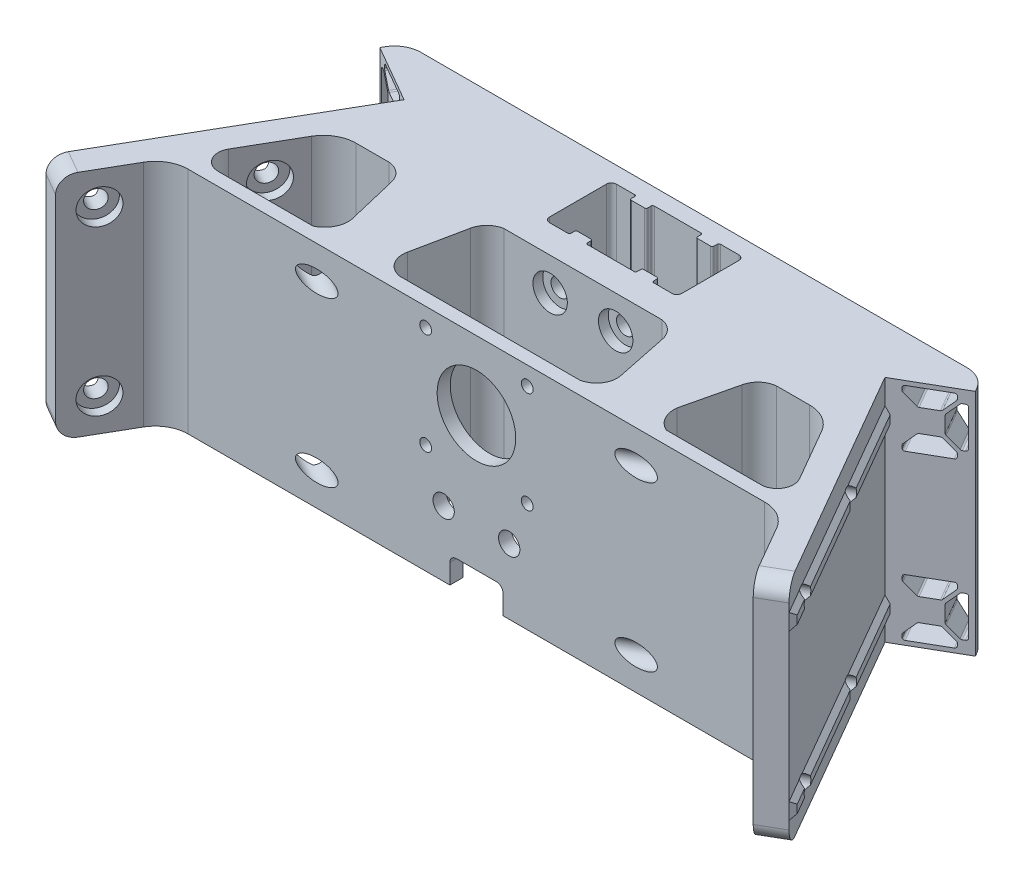
SolidWorks part; units mm, degrees
ref_plane "Front Plane" through (0, 0, 0) normal (0, 0, 1) x (1, 0, 0)
ref_plane "Top Plane" through (0, 0, 0) normal (0, 1, 0) x (1, 0, 0)
ref_plane "Right Plane" through (0, 0, 0) normal (1, 0, 0) x (0, 0, -1)
sketch "Sketch1" plane through (0, 0, 0) normal (0, 1, 0) x (1, 0, 0)
  line L0 (0, -61.4) -> (0, -111.1933) construction
  line L1 (0, 0) -> (-7.6, 0) construction
  line L2 (0, 0) -> (0, -20.4) construction
  line L3 (0, -20.4) -> (-7.1, -20.4) construction
  line L4 (-20.2, 0) -> (-20.2, -20.4) construction
  line L5 (0, 5) -> (-83.3812, 5)
  line L6 (-90.3094, 1) -> (-90.8868, 0)
  line L7 (-90.8868, 0) -> (-73.393, -10.1)
  line L8 (-73.393, -10.1) -> (-113.393, -79.382)
  line L9 (-113.393, -79.382) -> (-106.4648, -83.382)
  line L10 (-106.4648, -83.382) -> (-96.6603, -66.4)
  line L11 (-69.2361, -28.9) -> (0, -28.9)
  line L12 (0, -57.4) -> (0, -61.4)
  line L13 (0, -20.4) -> (-7.1, -20.4)
  line L14 (-20.2, -18.9) -> (-20.2, -1.5)
  line L15 (-18.7, 0) -> (-13.1, 0)
  line L16 (-82.8038, -57.4) -> (0, -57.4)
  line L17 (0, -20.4) -> (0, -28.9)
  line L18 (0, -61.4) -> (-88, -61.4)
  line L19 (-87.134, -49.9) -> (-77.8964, -33.9)
  line L20 (0, 0) -> (0, -20.4) construction
  line L21 (-7.6, -0.5) -> (-7.6, -1.5)
  line L22 (-20.2, -10.2) -> (0, -10.2) construction
  line L23 (-8.1, -2) -> (-12.1, -2)
  line L24 (-12.6, -0.5) -> (-12.6, -1.5)
  line L25 (-12.6, -19.9) -> (-12.6, -18.9)
  line L26 (-8.1, -18.4) -> (-12.1, -18.4)
  line L27 (-12.6, 0) -> (-20.2, 0) construction
  line L28 (-7.1, 0) -> (0, 0)
  line L29 (-7.6, -19.9) -> (-7.6, -18.9)
  line L30 (-13.1, -20.4) -> (-20.2, -20.4) construction
  line L31 (-13.1, -20.4) -> (-18.7, -20.4)
  line L32 (0, -28.9) -> (0, -57.4) construction
  line L33 (0, 5) -> (0, 0)
  arc A0 (-88, -61.4) -> (-96.6603, -66.4) centre (-88, -71.4) ccw
  arc A1 (-77.8964, -33.9) -> (-69.2361, -28.9) centre (-69.2361, -38.9) cw
  arc A2 (-82.8038, -57.4) -> (-87.134, -49.9) centre (-82.8038, -52.4) cw
  arc A3 (-83.3812, 5) -> (-90.3094, 1) centre (-83.3812, -3) ccw
  arc A4 (-7.1, 0) -> (-7.6, -0.5) centre (-7.1, -0.5) ccw
  arc A5 (-12.6, -0.5) -> (-13.1, 0) centre (-13.1, -0.5) ccw
  arc A6 (-7.6, -1.5) -> (-8.1, -2) centre (-8.1, -1.5) cw
  arc A7 (-12.1, -2) -> (-12.6, -1.5) centre (-12.1, -1.5) cw
  arc A8 (-20.2, -1.5) -> (-18.7, 0) centre (-18.7, -1.5) cw
  arc A9 (-18.7, -20.4) -> (-20.2, -18.9) centre (-18.7, -18.9) cw
  arc A10 (-12.1, -18.4) -> (-12.6, -18.9) centre (-12.1, -18.9) ccw
  arc A11 (-7.6, -18.9) -> (-8.1, -18.4) centre (-8.1, -18.9) ccw
  arc A12 (-12.6, -19.9) -> (-13.1, -20.4) centre (-13.1, -19.9) cw
  arc A13 (-7.1, -20.4) -> (-7.6, -19.9) centre (-7.1, -19.9) cw
  point P24 (-91.4641, -57.4)
  point P27 (-88, 5)
  point P30 (-10.1, 0)
  point P63 (-10.1, -20.4)
  dimension "D13" = 10
  dimension "D14" = 5
  dimension "D15" = 8
  dimension "D17" = 0.5
  dimension "D18" = 1.5
  dimension "D1" = 20.2
  dimension "D2" = 20.4
  dimension "D3" = 5
  dimension "D4" = 88
  dimension "D5" = 120
  dimension "D6" = 5
  dimension "D7" = 20.2
  dimension "D8" = 80
  dimension "D9" = 8
  dimension "D10" = 8.5
  dimension "D11" = 4
  dimension "D12" = 37
  dimension "D16" = 5
extrude "Boss-Extrude2" add sketch "Sketch1" along normal blind 70
sketch "Sketch2" plane through (-50.6714, 0, -29.2551) normal (-0.866, 0, -0.5) x (-0.5, 0, 0.866)
  line L0 (45.4434, 70) -> (45.4434, 0) construction
  line L1 (45.4434, 62.5) -> (125.4434, 62.5)
  line L2 (45.4434, 62.5) -> (45.4434, 57.5)
  line L3 (45.4434, 57.5) -> (125.4434, 57.5)
  line L4 (125.4434, 62.5) -> (125.4434, 57.5)
  line L5 (125.4434, 70) -> (125.4434, 0) construction
  line L6 (45.4434, 70) -> (125.4434, 70) construction
  line L7 (45.4434, 35) -> (125.4434, 35) construction
  line L8 (125.4434, 7.5) -> (125.4434, 12.5)
  line L9 (45.4434, 12.5) -> (125.4434, 12.5)
  line L10 (45.4434, 7.5) -> (45.4434, 12.5)
  line L11 (45.4434, 7.5) -> (125.4434, 7.5)
  dimension "D1" = 5
  dimension "D2" = 7.5
extrude "Boss-Extrude3" add sketch "Sketch2" along normal blind 1.5 draft 40
hole_wizard "CBORE for M5 SHCS2" positions "Sketch5" profile "Sketch4" counterbore size "M5" standard "ANSI Metric" end condition up to next
sketch "Sketch5" plane through (-43.7431, 0, -25.2551) normal (0.866, 0, 0.5) x (0.5, 0, -0.866)
  line L0 (-125.4434, 60) -> (-68.3064, 60) construction
  line L1 (-125.4434, 70) -> (-125.4434, 0) construction
  line L2 (-68.3064, 70) -> (-68.3064, 0) construction
  line L4 (-86.7817, 70) -> (-68.3064, 70) construction
  line L5 (-125.4434, 10) -> (-68.3064, 10) construction
  line L7 (-125.4434, 0) -> (-105.8342, 0) construction
  line L10 (-125.4434, 70) -> (-105.8342, 70) construction
  line L11 (-115.6388, 70) -> (-115.6388, 60) construction
  line L13 (-77.5441, 70) -> (-77.5441, 60) construction
  point P0 (-77.5441, 60)
  point P2 (-77.5441, 10)
  point P4 (-115.6388, 60)
  point P6 (-115.6388, 10)
  dimension "D1" = 10
  dimension "D2" = 10
sketch "Sketch4" plane through (-82.5152, 60, 41.9) normal (0, 1, 0) x (0.5, 0, -0.866)
  line L0 (0, 0) -> (0, 9.5)
  line L1 (0, 9.5) -> (2.75, 9.5)
  line L3 (2.75, 9.5) -> (2.75, 3)
  line L4 (2.75, 3) -> (5.25, 3)
  line L5 (5.25, 3) -> (5.25, 0)
  line L7 (5.25, 0) -> (0, 0)
  line L11 (0, -6.35) -> (0, 107.95) construction
  dimension "Thru Hole Dia." = 5.5
  dimension "Thru Hole Depth" = 9.5
  dimension "C'Bore Dia." = 10.5
  dimension "C'Bore Depth" = 3
hole_wizard "CBORE for M5 SHCS3" positions "Sketch7" profile "Sketch6" counterbore size "M5" standard "ANSI Metric" end condition up to next
sketch "Sketch7" plane through (0, 0, 28.9) normal (0, 0, 1) x (1, 0, 0)
  line L0 (0, 60) -> (0, 0) construction
  line L1 (-69.2361, 70) -> (0, 70) construction
  line L2 (-69.2361, 0) -> (0, 0) construction
  line L4 (0, 60) -> (-28.3411, 60)
  line L6 (0, 20) -> (-25.3792, 20) construction
  line L8 (-69.2361, 0) -> (0, 0) construction
  line L10 (0, 70) -> (0, 0) construction
  point P0 (-10, 20)
  point P2 (-10, 60)
  dimension "D1" = 10
  dimension "D2" = 10
  dimension "D3" = 20
sketch "Sketch6" plane through (-10, 20, 28.9) normal (1, 0, 0) x (0, -1, 0)
  line L0 (0, 0) -> (0, 10.5)
  line L1 (0, 10.5) -> (2.75, 10.5)
  line L3 (2.75, 10.5) -> (2.75, 3)
  line L4 (2.75, 3) -> (5.25, 3)
  line L5 (5.25, 3) -> (5.25, 0)
  line L7 (5.25, 0) -> (0, 0)
  line L11 (0, -6.35) -> (0, 107.95) construction
  dimension "Thru Hole Dia." = 5.5
  dimension "Thru Hole Depth" = 10.5
  dimension "C'Bore Dia." = 10.5
  dimension "C'Bore Depth" = 3
chamfer "Chamfer1" [suppressed] distance 5 angle 45
chamfer "Chamfer2" [suppressed] distance 5 angle 45
fillet "Fillet1" radius 5 2 edges at (-109.9289, 0, 81.382) (-109.9289, 70, 81.382)
sketch "Sketch14" plane through (-22.7217, 0, 39.3551) normal (-0.5, 0, 0.866) x (0.866, 0, 0.5)
  line L0 (-73.9972, 68.5) -> (-63.0232, 68.5)
  line L1 (-62.5152, 67.992) -> (-62.5152, 67.2661)
  line L2 (-65.7671, 63.8038) -> (-62.664, 66.9069)
  line L3 (-66.1263, 63.655) -> (-70.8942, 63.655)
  line L12 (-74.5052, 67.992) -> (-74.5052, 67.2661)
  line L13 (-74.3564, 66.9069) -> (-71.2534, 63.8038)
  line L14 (-77.0102, 65.487) -> (-77.0102, 54.513)
  line L15 (-76.5022, 54.005) -> (-75.7763, 54.005)
  line L16 (-75.4171, 54.1538) -> (-72.314, 57.2569)
  line L17 (-72.1652, 57.6161) -> (-72.1652, 62.3839)
  line L18 (-72.314, 62.7431) -> (-75.4171, 65.8462)
  line L19 (-75.7763, 65.995) -> (-76.5022, 65.995)
  line L20 (-73.9972, 51.5) -> (-63.0232, 51.5)
  line L21 (-62.5152, 52.008) -> (-62.5152, 52.7339)
  line L22 (-62.664, 53.0931) -> (-65.7671, 56.1962)
  line L23 (-66.1263, 56.345) -> (-70.8942, 56.345)
  line L25 (-71.2534, 56.1962) -> (-74.3564, 53.0931)
  line L26 (-74.5052, 52.7339) -> (-74.5052, 52.008)
  line L52 (-74.5052, 52.008) -> (-74.5052, 52.7339)
  line L53 (-71.6482, 51.5) -> (-73.9972, 51.5)
  line L54 (-71.1402, 50.508) -> (-71.1402, 50.992)
  line L55 (-77.0102, 50) -> (-71.6482, 50)
  line L56 (-78.5102, 56.862) -> (-78.5102, 51.5)
  line L57 (-77.5182, 57.37) -> (-78.0022, 57.37)
  line L58 (-77.0102, 54.513) -> (-77.0102, 56.862)
  line L59 (-75.7763, 54.005) -> (-76.5022, 54.005)
  line L60 (-72.314, 57.2569) -> (-75.4171, 54.1538)
  line L61 (-72.1652, 62.3839) -> (-72.1652, 57.6161)
  line L62 (-75.4171, 65.8462) -> (-72.314, 62.7431)
  line L63 (-76.5022, 65.995) -> (-75.7763, 65.995)
  line L64 (-77.0102, 63.138) -> (-77.0102, 65.487)
  line L65 (-78.0022, 62.63) -> (-77.5182, 62.63)
  line L66 (-78.5102, 68.5) -> (-78.5102, 63.138)
  line L67 (-71.6482, 70) -> (-77.0102, 70)
  line L68 (-71.1402, 69.008) -> (-71.1402, 69.492)
  line L69 (-73.9972, 68.5) -> (-71.6482, 68.5)
  line L70 (-74.5052, 67.2661) -> (-74.5052, 67.992)
  line L71 (-71.2534, 63.8038) -> (-74.3564, 66.9069)
  line L72 (-66.1263, 63.655) -> (-70.8942, 63.655)
  line L73 (-62.664, 66.9069) -> (-65.7671, 63.8038)
  line L74 (-62.5152, 67.992) -> (-62.5152, 67.2661)
  line L75 (-65.3722, 68.5) -> (-63.0232, 68.5)
  line L76 (-65.8802, 69.492) -> (-65.8802, 69.008)
  line L77 (-60.0102, 70) -> (-65.3722, 70)
  line L78 (-58.5102, 63.138) -> (-58.5102, 68.5)
  line L79 (-59.5022, 62.63) -> (-59.0182, 62.63)
  line L80 (-60.0102, 65.487) -> (-60.0102, 63.138)
  line L81 (-61.2442, 65.995) -> (-60.5182, 65.995)
  line L82 (-64.7064, 62.7431) -> (-61.6034, 65.8462)
  line L83 (-64.8552, 57.6161) -> (-64.8552, 62.3839)
  line L84 (-61.6034, 54.1538) -> (-64.7064, 57.2569)
  line L85 (-60.5182, 54.005) -> (-61.2442, 54.005)
  line L86 (-60.0102, 56.862) -> (-60.0102, 54.513)
  line L87 (-59.0182, 57.37) -> (-59.5022, 57.37)
  line L88 (-58.5102, 51.5) -> (-58.5102, 56.862)
  line L89 (-65.3722, 50) -> (-60.0102, 50)
  line L90 (-65.8802, 50.992) -> (-65.8802, 50.508)
  line L91 (-63.0232, 51.5) -> (-65.3722, 51.5)
  line L92 (-62.5152, 52.7339) -> (-62.5152, 52.008)
  line L93 (-65.7671, 56.1962) -> (-62.664, 53.0931)
  line L94 (-70.8942, 56.345) -> (-66.1263, 56.345)
  line L95 (-74.3564, 53.0931) -> (-71.2534, 56.1962)
  line L96 (-74.5052, 52.008) -> (-74.5052, 52.7339) construction
  line L97 (-71.6482, 51.5) -> (-73.9972, 51.5) construction
  line L98 (-71.1402, 50.508) -> (-71.1402, 50.992) construction
  line L99 (-77.0102, 50) -> (-71.6482, 50) construction
  line L100 (-78.5102, 56.862) -> (-78.5102, 51.5) construction
  line L101 (-77.5182, 57.37) -> (-78.0022, 57.37) construction
  line L102 (-77.0102, 54.513) -> (-77.0102, 56.862) construction
  line L103 (-75.7763, 54.005) -> (-76.5022, 54.005) construction
  line L104 (-72.314, 57.2569) -> (-75.4171, 54.1538) construction
  line L105 (-72.1652, 62.3839) -> (-72.1652, 57.6161) construction
  line L106 (-75.4171, 65.8462) -> (-72.314, 62.7431) construction
  line L107 (-76.5022, 65.995) -> (-75.7763, 65.995) construction
  line L108 (-77.0102, 63.138) -> (-77.0102, 65.487) construction
  line L109 (-78.0022, 62.63) -> (-77.5182, 62.63) construction
  line L110 (-78.5102, 68.5) -> (-78.5102, 63.138) construction
  line L111 (-71.6482, 70) -> (-77.0102, 70) construction
  line L112 (-71.1402, 69.008) -> (-71.1402, 69.492) construction
  line L113 (-73.9972, 68.5) -> (-71.6482, 68.5) construction
  line L114 (-74.5052, 67.2661) -> (-74.5052, 67.992) construction
  line L115 (-71.2534, 63.8038) -> (-74.3564, 66.9069) construction
  line L116 (-66.1263, 63.655) -> (-70.8942, 63.655) construction
  line L117 (-62.664, 66.9069) -> (-65.7671, 63.8038) construction
  line L118 (-62.5152, 67.992) -> (-62.5152, 67.2661) construction
  line L119 (-65.3722, 68.5) -> (-63.0232, 68.5) construction
  line L120 (-65.8802, 69.492) -> (-65.8802, 69.008) construction
  line L121 (-60.0102, 70) -> (-65.3722, 70) construction
  line L122 (-58.5102, 63.138) -> (-58.5102, 68.5) construction
  line L123 (-59.5022, 62.63) -> (-59.0182, 62.63) construction
  line L124 (-60.0102, 65.487) -> (-60.0102, 63.138) construction
  line L125 (-61.2442, 65.995) -> (-60.5182, 65.995) construction
  line L126 (-64.7064, 62.7431) -> (-61.6034, 65.8462) construction
  line L127 (-64.8552, 57.6161) -> (-64.8552, 62.3839) construction
  line L128 (-61.6034, 54.1538) -> (-64.7064, 57.2569) construction
  line L129 (-60.5182, 54.005) -> (-61.2442, 54.005) construction
  line L130 (-60.0102, 56.862) -> (-60.0102, 54.513) construction
  line L131 (-59.0182, 57.37) -> (-59.5022, 57.37) construction
  line L132 (-58.5102, 51.5) -> (-58.5102, 56.862) construction
  line L133 (-65.3722, 50) -> (-60.0102, 50) construction
  line L134 (-65.8802, 50.992) -> (-65.8802, 50.508) construction
  line L135 (-63.0232, 51.5) -> (-65.3722, 51.5) construction
  line L136 (-62.5152, 52.7339) -> (-62.5152, 52.008) construction
  line L137 (-65.7671, 56.1962) -> (-62.664, 53.0931) construction
  line L138 (-70.8942, 56.345) -> (-66.1263, 56.345) construction
  line L139 (-74.3564, 53.0931) -> (-71.2534, 56.1962) construction
  arc A0 (-74.5052, 67.992) -> (-73.9972, 68.5) centre (-73.9972, 67.992) cw
  arc A1 (-74.3564, 66.9069) -> (-74.5052, 67.2661) centre (-73.9972, 67.2661) cw
  arc A2 (-71.2534, 63.8038) -> (-70.8942, 63.655) centre (-70.8942, 64.163) ccw
  arc A3 (-66.1263, 63.655) -> (-65.7671, 63.8038) centre (-66.1263, 64.163) ccw
  arc A4 (-62.664, 66.9069) -> (-62.5152, 67.2661) centre (-63.0232, 67.2661) ccw
  arc A5 (-62.5152, 67.992) -> (-63.0232, 68.5) centre (-63.0232, 67.992) ccw
  arc A6 (-77.0102, 54.513) -> (-76.5022, 54.005) centre (-76.5022, 54.513) ccw
  arc A7 (-75.7763, 54.005) -> (-75.4171, 54.1538) centre (-75.7763, 54.513) ccw
  arc A8 (-72.314, 57.2569) -> (-72.1652, 57.6161) centre (-72.6732, 57.6161) ccw
  arc A9 (-72.1652, 62.3839) -> (-72.314, 62.7431) centre (-72.6732, 62.3839) ccw
  arc A10 (-75.4171, 65.8462) -> (-75.7763, 65.995) centre (-75.7763, 65.487) ccw
  arc A11 (-76.5022, 65.995) -> (-77.0102, 65.487) centre (-76.5022, 65.487) ccw
  arc A36 (-63.0232, 51.5) -> (-62.5152, 52.008) centre (-63.0232, 52.008) ccw
  arc A37 (-62.5152, 52.7339) -> (-62.664, 53.0931) centre (-63.0232, 52.7339) ccw
  arc A38 (-65.7671, 56.1962) -> (-66.1263, 56.345) centre (-66.1263, 55.837) ccw
  arc A39 (-74.3564, 53.0931) -> (-74.5052, 52.7339) centre (-73.9972, 52.7339) ccw
  arc A40 (-74.5052, 52.008) -> (-73.9972, 51.5) centre (-73.9972, 52.008) ccw
  arc A41 (-70.8942, 56.345) -> (-71.2534, 56.1962) centre (-70.8942, 55.837) ccw
  arc A68 (-74.5052, 52.008) -> (-73.9972, 51.5) centre (-73.9972, 52.008) ccw
  arc A69 (-71.1402, 50.992) -> (-71.6482, 51.5) centre (-71.6482, 50.992) ccw
  arc A70 (-71.6482, 50) -> (-71.1402, 50.508) centre (-71.6482, 50.508) ccw
  arc A71 (-78.5102, 51.5) -> (-77.0102, 50) centre (-77.0102, 51.5) ccw
  arc A72 (-78.0022, 57.37) -> (-78.5102, 56.862) centre (-78.0022, 56.862) ccw
  arc A73 (-77.0102, 56.862) -> (-77.5182, 57.37) centre (-77.5182, 56.862) ccw
  arc A74 (-77.0102, 54.513) -> (-76.5022, 54.005) centre (-76.5022, 54.513) ccw
  arc A75 (-75.7763, 54.005) -> (-75.4171, 54.1538) centre (-75.7763, 54.513) ccw
  arc A76 (-72.314, 57.2569) -> (-72.1652, 57.6161) centre (-72.6732, 57.6161) ccw
  arc A77 (-72.1652, 62.3839) -> (-72.314, 62.7431) centre (-72.6732, 62.3839) ccw
  arc A78 (-75.4171, 65.8462) -> (-75.7763, 65.995) centre (-75.7763, 65.487) ccw
  arc A79 (-76.5022, 65.995) -> (-77.0102, 65.487) centre (-76.5022, 65.487) ccw
  arc A80 (-77.5182, 62.63) -> (-77.0102, 63.138) centre (-77.5182, 63.138) ccw
  arc A81 (-78.5102, 63.138) -> (-78.0022, 62.63) centre (-78.0022, 63.138) ccw
  arc A82 (-77.0102, 70) -> (-78.5102, 68.5) centre (-77.0102, 68.5) ccw
  arc A83 (-71.1402, 69.492) -> (-71.6482, 70) centre (-71.6482, 69.492) ccw
  arc A84 (-71.6482, 68.5) -> (-71.1402, 69.008) centre (-71.6482, 69.008) ccw
  arc A85 (-73.9972, 68.5) -> (-74.5052, 67.992) centre (-73.9972, 67.992) ccw
  arc A86 (-74.5052, 67.2661) -> (-74.3564, 66.9069) centre (-73.9972, 67.2661) ccw
  arc A87 (-71.2534, 63.8038) -> (-70.8942, 63.655) centre (-70.8942, 64.163) ccw
  arc A88 (-66.1263, 63.655) -> (-65.7671, 63.8038) centre (-66.1263, 64.163) ccw
  arc A89 (-62.664, 66.9069) -> (-62.5152, 67.2661) centre (-63.0232, 67.2661) ccw
  arc A90 (-62.5152, 67.992) -> (-63.0232, 68.5) centre (-63.0232, 67.992) ccw
  arc A91 (-65.8802, 69.008) -> (-65.3722, 68.5) centre (-65.3722, 69.008) ccw
  arc A92 (-65.3722, 70) -> (-65.8802, 69.492) centre (-65.3722, 69.492) ccw
  arc A93 (-58.5102, 68.5) -> (-60.0102, 70) centre (-60.0102, 68.5) ccw
  arc A94 (-59.0182, 62.63) -> (-58.5102, 63.138) centre (-59.0182, 63.138) ccw
  arc A95 (-60.0102, 63.138) -> (-59.5022, 62.63) centre (-59.5022, 63.138) ccw
  arc A96 (-60.0102, 65.487) -> (-60.5182, 65.995) centre (-60.5182, 65.487) ccw
  arc A97 (-61.2442, 65.995) -> (-61.6034, 65.8462) centre (-61.2442, 65.487) ccw
  arc A98 (-64.7064, 62.7431) -> (-64.8552, 62.3839) centre (-64.3472, 62.3839) ccw
  arc A99 (-64.8552, 57.6161) -> (-64.7064, 57.2569) centre (-64.3472, 57.6161) ccw
  arc A100 (-61.6034, 54.1538) -> (-61.2442, 54.005) centre (-61.2442, 54.513) ccw
  arc A101 (-60.5182, 54.005) -> (-60.0102, 54.513) centre (-60.5182, 54.513) ccw
  arc A102 (-59.5022, 57.37) -> (-60.0102, 56.862) centre (-59.5022, 56.862) ccw
  arc A103 (-58.5102, 56.862) -> (-59.0182, 57.37) centre (-59.0182, 56.862) ccw
  arc A104 (-60.0102, 50) -> (-58.5102, 51.5) centre (-60.0102, 51.5) ccw
  arc A105 (-65.8802, 50.508) -> (-65.3722, 50) centre (-65.3722, 50.508) ccw
  arc A106 (-65.3722, 51.5) -> (-65.8802, 50.992) centre (-65.3722, 50.992) ccw
  arc A107 (-63.0232, 51.5) -> (-62.5152, 52.008) centre (-63.0232, 52.008) ccw
  arc A108 (-62.5152, 52.7339) -> (-62.664, 53.0931) centre (-63.0232, 52.7339) ccw
  arc A109 (-65.7671, 56.1962) -> (-66.1263, 56.345) centre (-66.1263, 55.837) ccw
  arc A110 (-70.8942, 56.345) -> (-71.2534, 56.1962) centre (-70.8942, 55.837) ccw
  arc A111 (-74.3564, 53.0931) -> (-74.5052, 52.7339) centre (-73.9972, 52.7339) ccw
  arc A112 (-74.5052, 52.008) -> (-73.9972, 51.5) centre (-73.9972, 52.008) ccw construction
  arc A113 (-71.1402, 50.992) -> (-71.6482, 51.5) centre (-71.6482, 50.992) ccw construction
  arc A114 (-71.6482, 50) -> (-71.1402, 50.508) centre (-71.6482, 50.508) ccw construction
  arc A115 (-78.5102, 51.5) -> (-77.0102, 50) centre (-77.0102, 51.5) ccw construction
  arc A116 (-78.0022, 57.37) -> (-78.5102, 56.862) centre (-78.0022, 56.862) ccw construction
  arc A117 (-77.0102, 56.862) -> (-77.5182, 57.37) centre (-77.5182, 56.862) ccw construction
  arc A118 (-77.0102, 54.513) -> (-76.5022, 54.005) centre (-76.5022, 54.513) ccw construction
  arc A119 (-75.7763, 54.005) -> (-75.4171, 54.1538) centre (-75.7763, 54.513) ccw construction
  arc A120 (-72.314, 57.2569) -> (-72.1652, 57.6161) centre (-72.6732, 57.6161) ccw construction
  arc A121 (-72.1652, 62.3839) -> (-72.314, 62.7431) centre (-72.6732, 62.3839) ccw construction
  arc A122 (-75.4171, 65.8462) -> (-75.7763, 65.995) centre (-75.7763, 65.487) ccw construction
  arc A123 (-76.5022, 65.995) -> (-77.0102, 65.487) centre (-76.5022, 65.487) ccw construction
  arc A124 (-77.5182, 62.63) -> (-77.0102, 63.138) centre (-77.5182, 63.138) ccw construction
  arc A125 (-78.5102, 63.138) -> (-78.0022, 62.63) centre (-78.0022, 63.138) ccw construction
  arc A126 (-77.0102, 70) -> (-78.5102, 68.5) centre (-77.0102, 68.5) ccw construction
  arc A127 (-71.1402, 69.492) -> (-71.6482, 70) centre (-71.6482, 69.492) ccw construction
  arc A128 (-71.6482, 68.5) -> (-71.1402, 69.008) centre (-71.6482, 69.008) ccw construction
  arc A129 (-73.9972, 68.5) -> (-74.5052, 67.992) centre (-73.9972, 67.992) ccw construction
  arc A130 (-74.5052, 67.2661) -> (-74.3564, 66.9069) centre (-73.9972, 67.2661) ccw construction
  arc A131 (-71.2534, 63.8038) -> (-70.8942, 63.655) centre (-70.8942, 64.163) ccw construction
  arc A132 (-66.1263, 63.655) -> (-65.7671, 63.8038) centre (-66.1263, 64.163) ccw construction
  arc A133 (-62.664, 66.9069) -> (-62.5152, 67.2661) centre (-63.0232, 67.2661) ccw construction
  arc A134 (-62.5152, 67.992) -> (-63.0232, 68.5) centre (-63.0232, 67.992) ccw construction
  arc A135 (-65.8802, 69.008) -> (-65.3722, 68.5) centre (-65.3722, 69.008) ccw construction
  arc A136 (-65.3722, 70) -> (-65.8802, 69.492) centre (-65.3722, 69.492) ccw construction
  arc A137 (-58.5102, 68.5) -> (-60.0102, 70) centre (-60.0102, 68.5) ccw construction
  arc A138 (-59.0182, 62.63) -> (-58.5102, 63.138) centre (-59.0182, 63.138) ccw construction
  arc A139 (-60.0102, 63.138) -> (-59.5022, 62.63) centre (-59.5022, 63.138) ccw construction
  arc A140 (-60.0102, 65.487) -> (-60.5182, 65.995) centre (-60.5182, 65.487) ccw construction
  arc A141 (-61.2442, 65.995) -> (-61.6034, 65.8462) centre (-61.2442, 65.487) ccw construction
  arc A142 (-64.7064, 62.7431) -> (-64.8552, 62.3839) centre (-64.3472, 62.3839) ccw construction
  arc A143 (-64.8552, 57.6161) -> (-64.7064, 57.2569) centre (-64.3472, 57.6161) ccw construction
  arc A144 (-61.6034, 54.1538) -> (-61.2442, 54.005) centre (-61.2442, 54.513) ccw construction
  arc A145 (-60.5182, 54.005) -> (-60.0102, 54.513) centre (-60.5182, 54.513) ccw construction
  arc A146 (-59.5022, 57.37) -> (-60.0102, 56.862) centre (-59.5022, 56.862) ccw construction
  arc A147 (-58.5102, 56.862) -> (-59.0182, 57.37) centre (-59.0182, 56.862) ccw construction
  arc A148 (-60.0102, 50) -> (-58.5102, 51.5) centre (-60.0102, 51.5) ccw construction
  arc A149 (-65.8802, 50.508) -> (-65.3722, 50) centre (-65.3722, 50.508) ccw construction
  arc A150 (-65.3722, 51.5) -> (-65.8802, 50.992) centre (-65.3722, 50.992) ccw construction
  arc A151 (-63.0232, 51.5) -> (-62.5152, 52.008) centre (-63.0232, 52.008) ccw construction
  arc A152 (-62.5152, 52.7339) -> (-62.664, 53.0931) centre (-63.0232, 52.7339) ccw construction
  arc A153 (-65.7671, 56.1962) -> (-66.1263, 56.345) centre (-66.1263, 55.837) ccw construction
  arc A154 (-70.8942, 56.345) -> (-71.2534, 56.1962) centre (-70.8942, 55.837) ccw construction
  arc A155 (-74.3564, 53.0931) -> (-74.5052, 52.7339) centre (-73.9972, 52.7339) ccw construction
  dimension "D2" = 0
sketch "Sketch15" plane through (-22.7217, 0, 39.3551) normal (-0.5, 0, 0.866) x (0.866, 0, 0.5)
  line L0 (-77.2102, 65.487) -> (-77.2102, 54.513)
  line L1 (-76.5022, 53.805) -> (-75.7763, 53.805)
  line L2 (-75.2757, 54.0124) -> (-72.1726, 57.1154)
  line L3 (-71.9652, 57.6161) -> (-71.9652, 62.3839)
  line L4 (-72.1726, 62.8846) -> (-75.2757, 65.9876)
  line L5 (-75.7763, 66.195) -> (-76.5022, 66.195)
  line L6 (-77.0102, 65.487) -> (-77.0102, 54.513)
  line L7 (-76.5022, 54.005) -> (-75.7763, 54.005)
  line L8 (-75.4171, 54.1538) -> (-72.314, 57.2569)
  line L9 (-72.1652, 57.6161) -> (-72.1652, 62.3839)
  line L10 (-72.314, 62.7431) -> (-75.4171, 65.8462)
  line L11 (-75.7763, 65.995) -> (-76.5022, 65.995)
  line L12 (-77.0102, 65.487) -> (-77.0102, 54.513) construction
  line L13 (-76.5022, 54.005) -> (-75.7763, 54.005) construction
  line L14 (-75.4171, 54.1538) -> (-72.314, 57.2569) construction
  line L15 (-72.1652, 57.6161) -> (-72.1652, 62.3839) construction
  line L16 (-72.314, 62.7431) -> (-75.4171, 65.8462) construction
  line L17 (-75.7763, 65.995) -> (-76.5022, 65.995) construction
  line L18 (-63.0232, 68.5) -> (-73.9972, 68.5)
  line L19 (-74.5052, 67.992) -> (-74.5052, 67.2661)
  line L20 (-74.3564, 66.9069) -> (-71.2534, 63.8038)
  line L21 (-70.8942, 63.655) -> (-66.1263, 63.655)
  line L22 (-65.7671, 63.8038) -> (-62.664, 66.9069)
  line L23 (-62.5152, 67.2661) -> (-62.5152, 67.992)
  line L24 (-63.0232, 68.5) -> (-73.9972, 68.5) construction
  line L25 (-74.5052, 67.992) -> (-74.5052, 67.2661) construction
  line L26 (-74.3564, 66.9069) -> (-71.2534, 63.8038) construction
  line L27 (-70.8942, 63.655) -> (-66.1263, 63.655) construction
  line L28 (-65.7671, 63.8038) -> (-62.664, 66.9069) construction
  line L29 (-62.5152, 67.2661) -> (-62.5152, 67.992) construction
  line L30 (-73.9972, 51.5) -> (-63.0232, 51.5)
  line L31 (-74.5052, 52.7339) -> (-74.5052, 52.008)
  line L32 (-71.2534, 56.1962) -> (-74.3564, 53.0931)
  line L33 (-66.1263, 56.345) -> (-70.8942, 56.345)
  line L34 (-62.664, 53.0931) -> (-65.7671, 56.1962)
  line L35 (-62.5152, 52.008) -> (-62.5152, 52.7339)
  line L36 (-73.9972, 51.5) -> (-63.0232, 51.5) construction
  line L37 (-74.5052, 52.7339) -> (-74.5052, 52.008) construction
  line L38 (-71.2534, 56.1962) -> (-74.3564, 53.0931) construction
  line L39 (-66.1263, 56.345) -> (-70.8942, 56.345) construction
  line L40 (-62.664, 53.0931) -> (-65.7671, 56.1962) construction
  line L41 (-62.5152, 52.008) -> (-62.5152, 52.7339) construction
  line L42 (-63.0232, 68.7) -> (-73.9972, 68.7)
  line L43 (-74.7052, 67.992) -> (-74.7052, 67.2661)
  line L44 (-74.4979, 66.7654) -> (-71.3948, 63.6624)
  line L45 (-70.8942, 63.455) -> (-66.1263, 63.455)
  line L46 (-65.6257, 63.6624) -> (-62.5226, 66.7654)
  line L47 (-62.3152, 67.2661) -> (-62.3152, 67.992)
  line L48 (-73.9972, 51.3) -> (-63.0232, 51.3)
  line L49 (-62.3152, 52.008) -> (-62.3152, 52.7339)
  line L50 (-62.5226, 53.2346) -> (-65.6257, 56.3376)
  line L51 (-66.1263, 56.545) -> (-70.8942, 56.545)
  line L52 (-71.3948, 56.3376) -> (-74.4979, 53.2346)
  line L53 (-74.7052, 52.7339) -> (-74.7052, 52.008)
  line L54 (-58.5102, 35) -> (-78.7102, 35) construction
  line L55 (-58.5102, 57.5) -> (-58.5102, 12.5) construction
  line L56 (-78.7102, 70) -> (-78.7102, 0) construction
  line L57 (-62.5152, 17.992) -> (-62.5152, 17.2661) construction
  line L58 (-62.664, 16.9069) -> (-65.7671, 13.8038) construction
  line L59 (-66.1263, 13.655) -> (-70.8942, 13.655) construction
  line L60 (-71.2534, 13.8038) -> (-74.3564, 16.9069) construction
  line L61 (-74.5052, 17.2661) -> (-74.5052, 17.992) construction
  line L62 (-73.9972, 18.5) -> (-63.0232, 18.5) construction
  line L63 (-62.5152, 2.7339) -> (-62.5152, 2.008) construction
  line L64 (-65.7671, 6.1962) -> (-62.664, 3.0931) construction
  line L65 (-70.8942, 6.345) -> (-66.1263, 6.345) construction
  line L66 (-74.3564, 3.0931) -> (-71.2534, 6.1962) construction
  line L67 (-74.5052, 2.008) -> (-74.5052, 2.7339) construction
  line L68 (-63.0232, 1.5) -> (-73.9972, 1.5) construction
  line L69 (-75.7763, 4.005) -> (-76.5022, 4.005) construction
  line L70 (-72.314, 7.2569) -> (-75.4171, 4.1538) construction
  line L71 (-72.1652, 12.3839) -> (-72.1652, 7.6161) construction
  line L72 (-75.4171, 15.8462) -> (-72.314, 12.7431) construction
  line L73 (-76.5022, 15.995) -> (-75.7763, 15.995) construction
  line L74 (-77.0102, 4.513) -> (-77.0102, 15.487) construction
  line L75 (-74.7052, 17.2661) -> (-74.7052, 17.992)
  line L76 (-71.3948, 13.6624) -> (-74.4979, 16.7654)
  line L77 (-66.1263, 13.455) -> (-70.8942, 13.455)
  line L78 (-62.5226, 16.7654) -> (-65.6257, 13.6624)
  line L79 (-62.3152, 17.992) -> (-62.3152, 17.2661)
  line L80 (-73.9972, 18.7) -> (-63.0232, 18.7)
  line L81 (-62.3152, 2.7339) -> (-62.3152, 2.008)
  line L82 (-65.6257, 6.3376) -> (-62.5226, 3.2346)
  line L83 (-70.8942, 6.545) -> (-66.1263, 6.545)
  line L84 (-74.4979, 3.2346) -> (-71.3948, 6.3376)
  line L85 (-74.7052, 2.008) -> (-74.7052, 2.7339)
  line L86 (-63.0232, 1.3) -> (-73.9972, 1.3)
  line L87 (-75.7763, 3.805) -> (-76.5022, 3.805)
  line L88 (-72.1726, 7.1154) -> (-75.2757, 4.0124)
  line L89 (-71.9652, 12.3839) -> (-71.9652, 7.6161)
  line L90 (-75.2757, 15.9876) -> (-72.1726, 12.8846)
  line L91 (-76.5022, 16.195) -> (-75.7763, 16.195)
  line L92 (-77.2102, 4.513) -> (-77.2102, 15.487)
  arc A0 (-77.2102, 54.513) -> (-76.5022, 53.805) centre (-76.5022, 54.513) ccw
  arc A1 (-75.7763, 53.805) -> (-75.2757, 54.0124) centre (-75.7763, 54.513) ccw
  arc A2 (-72.1726, 57.1154) -> (-71.9652, 57.6161) centre (-72.6732, 57.6161) ccw
  arc A3 (-71.9652, 62.3839) -> (-72.1726, 62.8846) centre (-72.6732, 62.3839) ccw
  arc A4 (-75.2757, 65.9876) -> (-75.7763, 66.195) centre (-75.7763, 65.487) ccw
  arc A5 (-76.5022, 66.195) -> (-77.2102, 65.487) centre (-76.5022, 65.487) ccw
  arc A6 (-77.0102, 54.513) -> (-76.5022, 54.005) centre (-76.5022, 54.513) ccw
  arc A7 (-75.7763, 54.005) -> (-75.4171, 54.1538) centre (-75.7763, 54.513) ccw
  arc A8 (-72.314, 57.2569) -> (-72.1652, 57.6161) centre (-72.6732, 57.6161) ccw
  arc A9 (-72.1652, 62.3839) -> (-72.314, 62.7431) centre (-72.6732, 62.3839) ccw
  arc A10 (-75.4171, 65.8462) -> (-75.7763, 65.995) centre (-75.7763, 65.487) ccw
  arc A11 (-76.5022, 65.995) -> (-77.0102, 65.487) centre (-76.5022, 65.487) ccw
  arc A12 (-77.0102, 54.513) -> (-76.5022, 54.005) centre (-76.5022, 54.513) ccw construction
  arc A13 (-75.7763, 54.005) -> (-75.4171, 54.1538) centre (-75.7763, 54.513) ccw construction
  arc A14 (-72.314, 57.2569) -> (-72.1652, 57.6161) centre (-72.6732, 57.6161) ccw construction
  arc A15 (-72.1652, 62.3839) -> (-72.314, 62.7431) centre (-72.6732, 62.3839) ccw construction
  arc A16 (-75.4171, 65.8462) -> (-75.7763, 65.995) centre (-75.7763, 65.487) ccw construction
  arc A17 (-76.5022, 65.995) -> (-77.0102, 65.487) centre (-76.5022, 65.487) ccw construction
  arc A18 (-73.9972, 68.5) -> (-74.5052, 67.992) centre (-73.9972, 67.992) ccw
  arc A19 (-74.5052, 67.2661) -> (-74.3564, 66.9069) centre (-73.9972, 67.2661) ccw
  arc A20 (-71.2534, 63.8038) -> (-70.8942, 63.655) centre (-70.8942, 64.163) ccw
  arc A21 (-66.1263, 63.655) -> (-65.7671, 63.8038) centre (-66.1263, 64.163) ccw
  arc A22 (-62.664, 66.9069) -> (-62.5152, 67.2661) centre (-63.0232, 67.2661) ccw
  arc A23 (-62.5152, 67.992) -> (-63.0232, 68.5) centre (-63.0232, 67.992) ccw
  arc A24 (-73.9972, 68.5) -> (-74.5052, 67.992) centre (-73.9972, 67.992) ccw construction
  arc A25 (-74.5052, 67.2661) -> (-74.3564, 66.9069) centre (-73.9972, 67.2661) ccw construction
  arc A26 (-71.2534, 63.8038) -> (-70.8942, 63.655) centre (-70.8942, 64.163) ccw construction
  arc A27 (-66.1263, 63.655) -> (-65.7671, 63.8038) centre (-66.1263, 64.163) ccw construction
  arc A28 (-62.664, 66.9069) -> (-62.5152, 67.2661) centre (-63.0232, 67.2661) ccw construction
  arc A29 (-62.5152, 67.992) -> (-63.0232, 68.5) centre (-63.0232, 67.992) ccw construction
  arc A30 (-74.5052, 52.008) -> (-73.9972, 51.5) centre (-73.9972, 52.008) ccw
  arc A31 (-74.3564, 53.0931) -> (-74.5052, 52.7339) centre (-73.9972, 52.7339) ccw
  arc A32 (-70.8942, 56.345) -> (-71.2534, 56.1962) centre (-70.8942, 55.837) ccw
  arc A33 (-65.7671, 56.1962) -> (-66.1263, 56.345) centre (-66.1263, 55.837) ccw
  arc A34 (-62.5152, 52.7339) -> (-62.664, 53.0931) centre (-63.0232, 52.7339) ccw
  arc A35 (-63.0232, 51.5) -> (-62.5152, 52.008) centre (-63.0232, 52.008) ccw
  arc A36 (-74.5052, 52.008) -> (-73.9972, 51.5) centre (-73.9972, 52.008) ccw construction
  arc A37 (-74.3564, 53.0931) -> (-74.5052, 52.7339) centre (-73.9972, 52.7339) ccw construction
  arc A38 (-70.8942, 56.345) -> (-71.2534, 56.1962) centre (-70.8942, 55.837) ccw construction
  arc A39 (-65.7671, 56.1962) -> (-66.1263, 56.345) centre (-66.1263, 55.837) ccw construction
  arc A40 (-62.5152, 52.7339) -> (-62.664, 53.0931) centre (-63.0232, 52.7339) ccw construction
  arc A41 (-63.0232, 51.5) -> (-62.5152, 52.008) centre (-63.0232, 52.008) ccw construction
  arc A42 (-73.9972, 68.7) -> (-74.7052, 67.992) centre (-73.9972, 67.992) ccw
  arc A43 (-74.7052, 67.2661) -> (-74.4979, 66.7654) centre (-73.9972, 67.2661) ccw
  arc A44 (-71.3948, 63.6624) -> (-70.8942, 63.455) centre (-70.8942, 64.163) ccw
  arc A45 (-66.1263, 63.455) -> (-65.6257, 63.6624) centre (-66.1263, 64.163) ccw
  arc A46 (-62.5226, 66.7654) -> (-62.3152, 67.2661) centre (-63.0232, 67.2661) ccw
  arc A47 (-62.3152, 67.992) -> (-63.0232, 68.7) centre (-63.0232, 67.992) ccw
  arc A48 (-63.0232, 51.3) -> (-62.3152, 52.008) centre (-63.0232, 52.008) ccw
  arc A49 (-62.3152, 52.7339) -> (-62.5226, 53.2346) centre (-63.0232, 52.7339) ccw
  arc A50 (-65.6257, 56.3376) -> (-66.1263, 56.545) centre (-66.1263, 55.837) ccw
  arc A51 (-70.8942, 56.545) -> (-71.3948, 56.3376) centre (-70.8942, 55.837) ccw
  arc A52 (-74.4979, 53.2346) -> (-74.7052, 52.7339) centre (-73.9972, 52.7339) ccw
  arc A53 (-74.7052, 52.008) -> (-73.9972, 51.3) centre (-73.9972, 52.008) ccw
  arc A54 (-63.0232, 18.5) -> (-62.5152, 17.992) centre (-63.0232, 17.992) cw construction
  arc A55 (-62.5152, 17.2661) -> (-62.664, 16.9069) centre (-63.0232, 17.2661) cw construction
  arc A56 (-65.7671, 13.8038) -> (-66.1263, 13.655) centre (-66.1263, 14.163) cw construction
  arc A57 (-70.8942, 13.655) -> (-71.2534, 13.8038) centre (-70.8942, 14.163) cw construction
  arc A58 (-74.3564, 16.9069) -> (-74.5052, 17.2661) centre (-73.9972, 17.2661) cw construction
  arc A59 (-74.5052, 17.992) -> (-73.9972, 18.5) centre (-73.9972, 17.992) cw construction
  arc A60 (-62.5152, 2.008) -> (-63.0232, 1.5) centre (-63.0232, 2.008) cw construction
  arc A61 (-62.664, 3.0931) -> (-62.5152, 2.7339) centre (-63.0232, 2.7339) cw construction
  arc A62 (-66.1263, 6.345) -> (-65.7671, 6.1962) centre (-66.1263, 5.837) cw construction
  arc A63 (-71.2534, 6.1962) -> (-70.8942, 6.345) centre (-70.8942, 5.837) cw construction
  arc A64 (-74.5052, 2.7339) -> (-74.3564, 3.0931) centre (-73.9972, 2.7339) cw construction
  arc A65 (-73.9972, 1.5) -> (-74.5052, 2.008) centre (-73.9972, 2.008) cw construction
  arc A66 (-76.5022, 4.005) -> (-77.0102, 4.513) centre (-76.5022, 4.513) cw construction
  arc A67 (-75.4171, 4.1538) -> (-75.7763, 4.005) centre (-75.7763, 4.513) cw construction
  arc A68 (-72.1652, 7.6161) -> (-72.314, 7.2569) centre (-72.6732, 7.6161) cw construction
  arc A69 (-72.314, 12.7431) -> (-72.1652, 12.3839) centre (-72.6732, 12.3839) cw construction
  arc A70 (-75.7763, 15.995) -> (-75.4171, 15.8462) centre (-75.7763, 15.487) cw construction
  arc A71 (-77.0102, 15.487) -> (-76.5022, 15.995) centre (-76.5022, 15.487) cw construction
  arc A72 (-74.7052, 17.992) -> (-73.9972, 18.7) centre (-73.9972, 17.992) cw
  arc A73 (-74.4979, 16.7654) -> (-74.7052, 17.2661) centre (-73.9972, 17.2661) cw
  arc A74 (-70.8942, 13.455) -> (-71.3948, 13.6624) centre (-70.8942, 14.163) cw
  arc A75 (-65.6257, 13.6624) -> (-66.1263, 13.455) centre (-66.1263, 14.163) cw
  arc A76 (-62.3152, 17.2661) -> (-62.5226, 16.7654) centre (-63.0232, 17.2661) cw
  arc A77 (-63.0232, 18.7) -> (-62.3152, 17.992) centre (-63.0232, 17.992) cw
  arc A78 (-62.3152, 2.008) -> (-63.0232, 1.3) centre (-63.0232, 2.008) cw
  arc A79 (-62.5226, 3.2346) -> (-62.3152, 2.7339) centre (-63.0232, 2.7339) cw
  arc A80 (-66.1263, 6.545) -> (-65.6257, 6.3376) centre (-66.1263, 5.837) cw
  arc A81 (-71.3948, 6.3376) -> (-70.8942, 6.545) centre (-70.8942, 5.837) cw
  arc A82 (-74.7052, 2.7339) -> (-74.4979, 3.2346) centre (-73.9972, 2.7339) cw
  arc A83 (-73.9972, 1.3) -> (-74.7052, 2.008) centre (-73.9972, 2.008) cw
  arc A84 (-76.5022, 3.805) -> (-77.2102, 4.513) centre (-76.5022, 4.513) cw
  arc A85 (-75.2757, 4.0124) -> (-75.7763, 3.805) centre (-75.7763, 4.513) cw
  arc A86 (-71.9652, 7.6161) -> (-72.1726, 7.1154) centre (-72.6732, 7.6161) cw
  arc A87 (-72.1726, 12.8846) -> (-71.9652, 12.3839) centre (-72.6732, 12.3839) cw
  arc A88 (-75.7763, 16.195) -> (-75.2757, 15.9876) centre (-75.7763, 15.487) cw
  arc A89 (-77.2102, 15.487) -> (-76.5022, 16.195) centre (-76.5022, 15.487) cw
  dimension "D1" = 0
  dimension "D2" = 0
  dimension "D3" = 0
  dimension "D4" = 0.2
extrude "Cut-Extrude5" cut sketch "Sketch15" against normal up to next
sketch "Sketch17" plane through (0, 0, 0) normal (0, 1, 0) x (1, 0, 0)
  line L0 (-77.8964, -33.9) -> (-8.392, -33.9) construction
  line L1 (0, -57.4) -> (-82.8038, -57.4) construction
  line L2 (-87.134, -49.9) -> (-8.392, -49.9) construction
  line L3 (-49.7313, -49.9) -> (-53.5337, -33.9)
  line L4 (-69.2361, -28.9) -> (0, -28.9) construction
  line L5 (-29.3026, -33.9) -> (-32.6088, -49.9)
  line L6 (-59.1642, -28.9) -> (-24.1454, -28.9)
  line L7 (-69.2361, -28.9) -> (-59.1642, -28.9) construction
  line L8 (-27.5009, -57.4) -> (-53.9252, -57.4)
  line L9 (-69.2361, -28.9) -> (0, -28.9) construction
  arc A0 (-29.3026, -33.9) -> (-24.1454, -28.9) centre (-23.047, -35.1926) cw
  arc A1 (-32.6088, -49.9) -> (-27.5009, -57.4) centre (-26.4248, -51.1778) ccw
  arc A2 (-53.5337, -33.9) -> (-59.1642, -28.9) centre (-59.7018, -35.1756) ccw
  arc A3 (-49.7313, -49.9) -> (-53.9252, -57.4) centre (-56.9594, -50.7807) cw
  point P22 (-53.9252, -57.4)
  point P25 (-60.4891, -28.9)
  point P26 (-60.4891, -28.9)
  point P29 (-25.9078, -57.4)
  point P32 (-22.3891, -28.9)
extrude "Boss-Extrude5" add sketch "Sketch17" along normal up to surface (70 mm away) up to face at (-34.1742, 70, 21.6107)
sketch "Sketch20" plane through (-43.7431, 0, -25.2551) normal (0.866, 0, 0.5) x (0.5, 0, -0.866)
  line L0 (-86.7817, 35) -> (-68.3064, 35) construction
  line L1 (-86.7817, 70) -> (-86.7817, 0) construction
  line L2 (-68.3064, 70) -> (-68.3064, 0) construction
  circle A0 centre (-77.5441, 60) radius 3.25
  circle A1 centre (-77.5441, 10) radius 3.25
  dimension "D1" = 6.5
extrude "Cut-Extrude7" cut sketch "Sketch20" along normal up to surface (44.6292 mm away)
mirror "Mirror1" about plane through (0, 70, 20.4) normal (-1, 0, 0) of bodies 116 102
sketch "Sketch8" plane through (0, 0, 57.4) normal (0, 0, -1) x (-1, 0, 0)
  line L0 (0, 0) -> (0, 69.4778) construction
  line L1 (88, 70) -> (-88, 70) construction
  circle A0 centre (0, 48.85) radius 12
  dimension "D1" = 24
  dimension "D2" = 21.15
extrude "Cut-Extrude2" cut sketch "Sketch8" along normal up to next (28.5 mm away) from surface at -4 starting at face at (-55.2402, 60, 61.4)
sketch "Sketch10" plane through (0, 0, 57.4) normal (0, 0, -1) x (-1, 0, 0)
  line L4 (27.5009, 0) -> (27.5009, 70)
  line L5 (27.5009, 0) -> (27.5009, 70)
  line L6 (27.5009, 70) -> (-27.5009, 70)
  line L7 (27.5009, 70) -> (-27.5009, 70)
  line L8 (-27.5009, 70) -> (-27.5009, 0)
  line L9 (-27.5009, 70) -> (-27.5009, 0)
  line L10 (-27.5009, 0) -> (27.5009, 0)
  line L11 (-27.5009, 0) -> (27.5009, 0)
  point P0 (-15.5, 33.35)
  point P2 (-15.5, 64.35)
  point P4 (15.5, 64.35)
  point P6 (15.5, 33.35)
  dimension "D1" = 0
hole_wizard "CBORE for M3 SHCS1" positions "3DSketch1" profile "Sketch11" counterbore size "M3" standard "ANSI Metric" end condition up to next
sketch3d "3DSketch1"
  point P0 (15.5, 33.35, 57.4)
  point P2 (-15.5, 33.35, 57.4)
  point P4 (-15.5, 64.35, 57.4)
  point P6 (15.5, 64.35, 57.4)
sketch "Sketch11" plane through (15.5, 33.35, 57.4) normal (1, 0, 0) x (0, 1, 0)
  line L0 (0, 0) -> (0, 4)
  line L1 (0, 4) -> (1.8, 4)
  line L3 (1.8, 4) -> (1.8, 1)
  line L4 (1.8, 1) -> (3.75, 1)
  line L5 (3.75, 1) -> (3.75, 0)
  line L7 (3.75, 0) -> (0, 0)
  line L11 (0, -6.35) -> (0, 107.95) construction
  dimension "Thru Hole Dia." = 3.6
  dimension "Thru Hole Depth" = 4
  dimension "C'Bore Dia." = 7.5
  dimension "C'Bore Depth" = 1
sketch "Sketch12" plane through (0, 0, 2) normal (0, 0, 1) x (1, 0, 0)
  line L0 (-8.1, 70) -> (-8.1, 0) construction
  line L1 (-12.1, 0) -> (-8.1, 0)
  line L2 (-12.1, 0) -> (-12.1, 8)
  line L3 (-12.1, 8) -> (-8.1, 8)
  line L4 (-8.1, 0) -> (-8.1, 8)
  line L5 (0, 0) -> (0, 25.5119) construction
  line L6 (8.1, 0) -> (8.1, 8)
  line L7 (12.1, 8) -> (8.1, 8)
  line L8 (12.1, 0) -> (12.1, 8)
  line L9 (12.1, 0) -> (8.1, 0)
  dimension "D1" = 8
extrude "Boss-Extrude4" add sketch "Sketch12" along normal up to next
sketch "Sketch13" plane through (0, 0, 28.9) normal (0, 0, 1) x (1, 0, 0)
  line L0 (-8.1, 0) -> (-8.1, 8) construction
  line L1 (-8.1, 0) -> (8.1, 0)
  line L2 (-8.1, 0) -> (-8.1, 6)
  line L3 (-6.1, 8) -> (6.1, 8)
  line L4 (8.1, 0) -> (8.1, 6)
  line L5 (-8.1, 8) -> (-12.1, 8) construction
  arc A0 (6.1, 8) -> (8.1, 6) centre (6.1, 6) cw
  arc A1 (-8.1, 6) -> (-6.1, 8) centre (-6.1, 6) cw
  dimension "D1" = 2
extrude "Cut-Extrude4" cut sketch "Sketch13" against normal up to next and the other way up to surface other way up to face at (13.7, 33.35, 61.4)
sketch "Sketch18" plane through (0, 0, 61.4) normal (0, 0, 1) x (1, 0, 0)
  circle A0 centre (10, 20) radius 5.25 construction
  circle A1 centre (-10, 20) radius 5.25 construction
  circle A2 centre (-10, 20) radius 5.25 construction
  circle A3 centre (10, 20) radius 5.25 construction
  circle A4 centre (-10, 20) radius 3.25
  circle A5 centre (10, 20) radius 3.25
  dimension "D1" = 2
  dimension "D2" = 6.5
extrude "Cut-Extrude6" cut sketch "Sketch18" against normal up to surface (4 mm away) up to face at (11.75, 33.35, 57.4)
